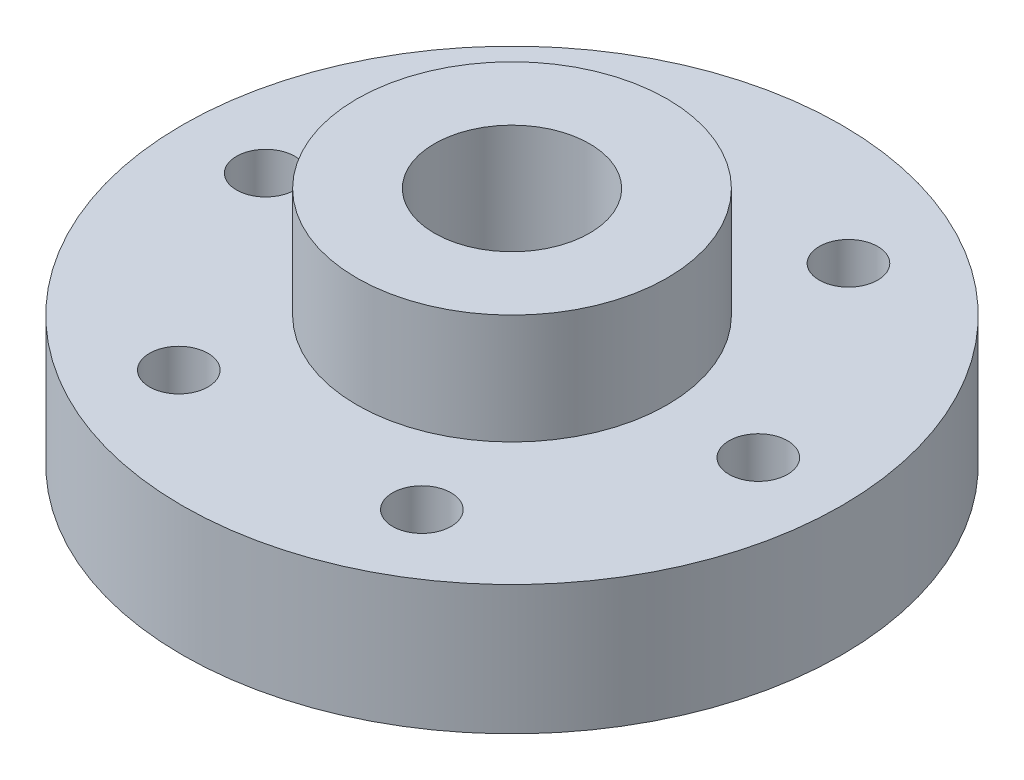
SolidWorks part; units mm, degrees
ref_plane "Front Plane" through (0, 0, 0) normal (0, 0, 1) x (1, 0, 0)
ref_plane "Top Plane" through (0, 0, 0) normal (0, 1, 0) x (1, 0, 0)
ref_plane "Right Plane" through (0, 0, 0) normal (1, 0, 0) x (0, 0, -1)
sketch "Sketch1" plane through (0, 0, 0) normal (0, 1, 0) x (1, 0, 0)
  circle A0 centre (0, 0) radius 12.75
  dimension "D1" = 25.5
extrude "Boss-Extrude1" add sketch "Sketch1" along normal blind 5
sketch "Sketch2" plane through (0, 5, 0) normal (0, 1, 0) x (1, 0, 0)
  circle A0 centre (0, 0) radius 6
  dimension "D1" = 12
extrude "Boss-Extrude2" add sketch "Sketch2" along normal blind 4.25
sketch "Sketch3" plane through (0, 9.25, 0) normal (0, 1, 0) x (1, 0, 0)
  circle A0 centre (0, 0) radius 3
extrude "Cut-Extrude1" cut sketch "Sketch3" against normal through all
sketch "Sketch4" plane through (0, 0, 0) normal (0, -1, 0) x (1, 0, 0)
  line L1 (9.525, 0) -> (4.7625, 8.2489)
  line L2 (4.7625, 8.2489) -> (-4.7625, 8.2489)
  line L3 (-4.7625, 8.2489) -> (-9.525, 0)
  line L4 (-9.525, 0) -> (-4.7625, -8.2489)
  line L5 (-4.7625, -8.2489) -> (4.7625, -8.2489)
  line L6 (4.7625, -8.2489) -> (9.525, 0)
  circle A0 centre (0, 0) radius 8.2489 construction
  dimension "D1" = 9.525
hole_wizard "#4-40 Tapped Hole2" positions "Sketch7" profile "Sketch8" tap size "#4-40" standard "ANSI Inch" end condition through all
sketch "Sketch7" plane through (0, 5, 0) normal (0, 1, 0) x (1, 0, 0)
  point P0 (-4.6097, -8.2771)
  point P2 (-9.525, 0)
  point P4 (4.7625, -8.2489)
  point P6 (9.525, 0)
  point P8 (-4.7625, 8.2489)
  point P11 (4.7625, 8.2489)
  point P15 (0, 0)
  point P17 (0, 0)
  point P19 (0, 0)
  point P21 (0, 0)
sketch "Sketch8" plane through (-4.6097, 5, 8.2771) normal (1, 0, 0) x (0, 0, 1)
  line L0 (0, 0) -> (0, 5)
  line L1 (0, 5) -> (1.1303, 5)
  line L2 (1.1303, 5) -> (1.1303, 0)
  line L5 (1.1303, 0) -> (0, 0)
  line L11 (0, -6.35) -> (0, 107.95) construction
  dimension "Thru Tap Drill Dia." = 2.2606
  dimension "Thru Tap Drill Depth" = 5
cosmetic thread "Hole Thread7" parameters "D2"=2.8448
cosmetic thread "Hole Thread8" parameters "D2"=2.8448
cosmetic thread "Hole Thread9" parameters "D2"=2.8448
cosmetic thread "Hole Thread10" parameters "D2"=2.8448
cosmetic thread "Hole Thread11" parameters "D2"=2.8448
cosmetic thread "Hole Thread12" parameters "D2"=2.8448
